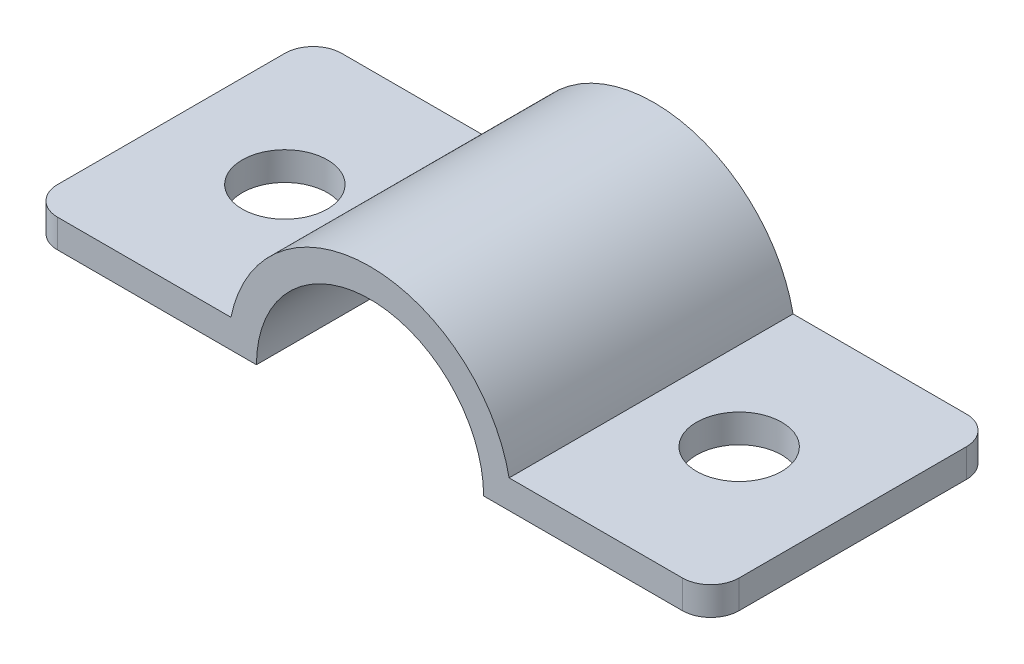
SolidWorks part; units mm, degrees
ref_plane "Front Plane" through (0, 0, 0) normal (0, 0, 1) x (1, 0, 0)
ref_plane "Top Plane" through (0, 0, 0) normal (0, 1, 0) x (1, 0, 0)
ref_plane "Right Plane" through (0, 0, 0) normal (1, 0, 0) x (0, 0, -1)
sketch "Sketch1" plane through (0, 0, 0) normal (0, 0, 1) x (1, 0, 0)
  line L0 (4, 0) -> (12, 0)
  line L1 (-4, 0) -> (-12, 0)
  line L2 (4.899, 1) -> (12, 1)
  line L3 (-4.899, 1) -> (-12, 1)
  line L4 (-12, 0) -> (-12, 1)
  line L5 (12, 0) -> (12, 1)
  arc A0 (4, 0) -> (-4, 0) centre (0, 0) ccw
  arc A1 (4.899, 1) -> (-4.899, 1) centre (0, 0) ccw
  dimension "D1" = 8
  dimension "D2" = 8
  dimension "D3" = 8
  dimension "D4" = 1
extrude "Boss-Extrude1" add sketch "Sketch1" along normal mid plane 10
fillet "Fillet1" radius 1 4 edges at (-12, 0.5, 5) (-12, 0.5, -5) (12, 0.5, -5) (12, 0.5, 5)
sketch "Sketch2" plane through (0, 1, 0) normal (0, 1, 0) x (1, 0, 0)
  line L0 (0, 0) -> (-8, 0) construction
  line L1 (0, -55) -> (0, 55) construction
  circle A0 centre (-8, 0) radius 1.5
  circle A1 centre (8, 0) radius 1.5
  dimension "D2" = 3
  dimension "D1" = 8
extrude "Cut-Extrude1" cut sketch "Sketch2" against normal blind 10
